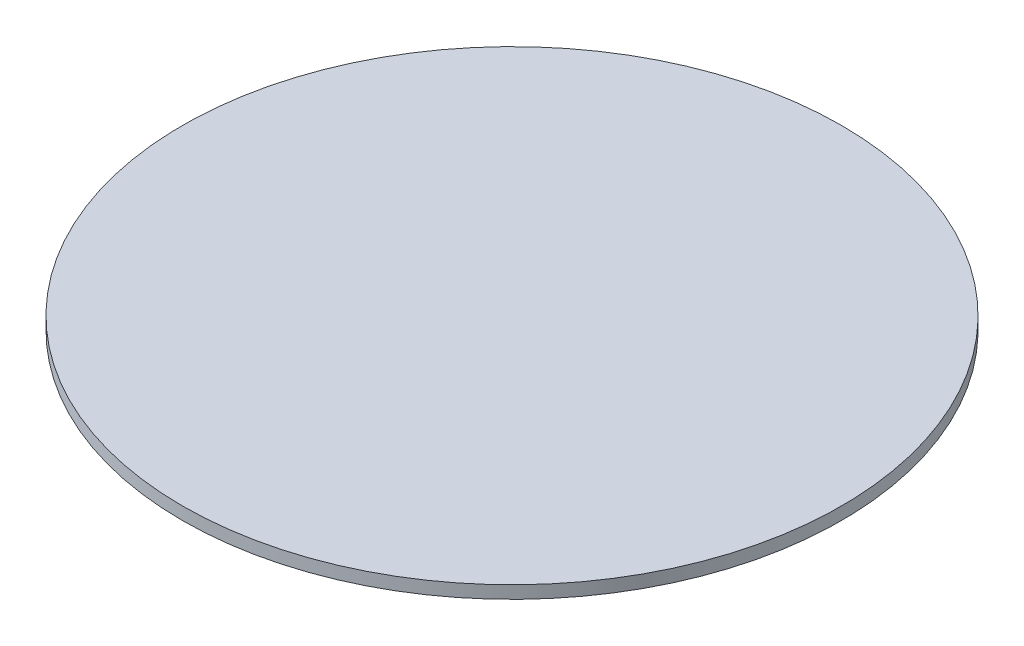
SolidWorks part; units mm, degrees
ref_plane "Front" through (0, 0, 0) normal (0, 0, 1) x (1, 0, 0)
ref_plane "Top" through (0, 0, 0) normal (0, 1, 0) x (1, 0, 0)
ref_plane "Right" through (0, 0, 0) normal (1, 0, 0) x (0, 0, -1)
sketch "Sketch1" plane through (0, 0, 0) normal (0, 1, 0) x (1, 0, 0)
  circle A0 centre (0, 0) radius 79.375
  dimension "D1" = 158.75
extrude "Boss-Extrude1" add sketch "Sketch1" along normal blind 3.048
